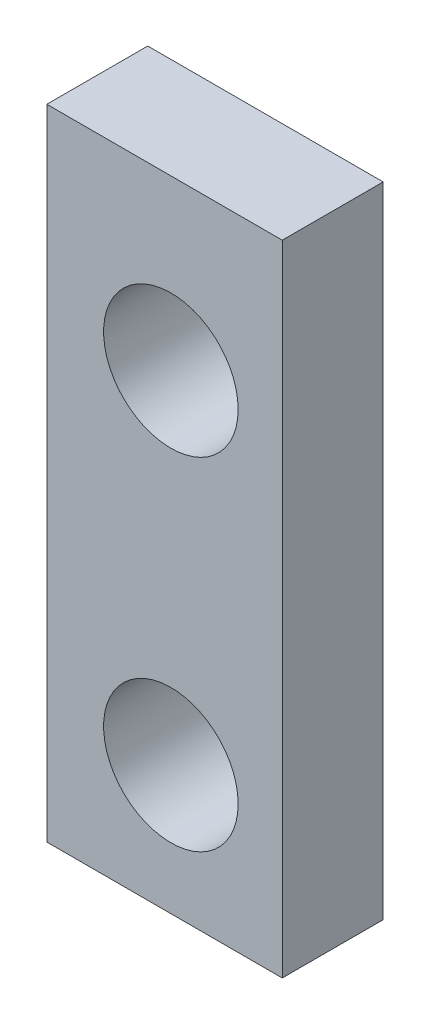
SolidWorks part; units mm, degrees
ref_plane "Front Plane" through (0, 0, 0) normal (0, 0, 1) x (1, 0, 0)
ref_plane "Top Plane" through (0, 0, 0) normal (0, 1, 0) x (1, 0, 0)
ref_plane "Right Plane" through (0, 0, 0) normal (1, 0, 0) x (0, 0, -1)
sketch "Sketch2" plane through (0, 0, 0) normal (0, 0, 1) x (1, 0, 0)
  line L0 (-13, 26.12) -> (-13, 6.12) construction
  line L1 (-20, 26.12) -> (-13, 26.12)
  line L2 (-20, 26.12) -> (-20, 7.12)
  line L3 (-20, 7.12) -> (-13, 7.12)
  line L4 (-13, 26.12) -> (-13, 7.12)
  circle A0 centre (-16.312, 21.106) radius 2
  circle A1 centre (-16.312, 10.946) radius 2
  dimension "D1" = 4
  dimension "D2" = 19
extrude "Boss-Extrude1" add sketch "Sketch2" along normal blind 3
